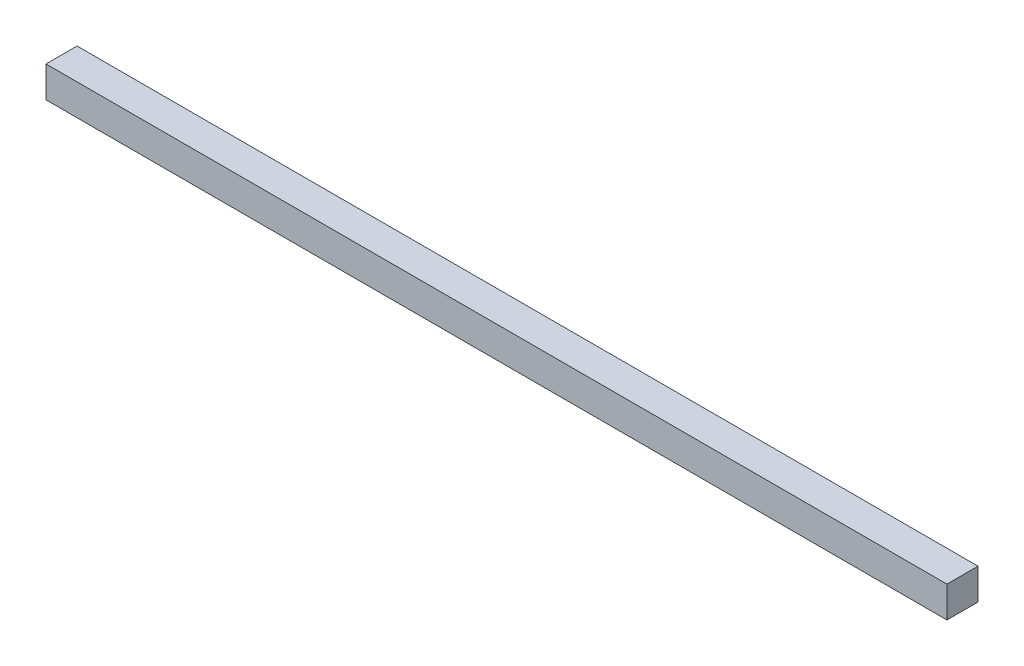
SolidWorks part; units mm, degrees
ref_plane "Front Plane" through (0, 0, 0) normal (0, 0, 1) x (1, 0, 0)
ref_plane "Top Plane" through (0, 0, 0) normal (0, 1, 0) x (1, 0, 0)
ref_plane "Right Plane" through (0, 0, 0) normal (1, 0, 0) x (0, 0, -1)
sketch "Sketch1" plane through (0, 0, 0) normal (0, 0, 1) x (1, 0, 0)
  line L1 (0, 0) -> (36.83, 0)
  line L2 (0, 0) -> (0, 1.27)
  line L3 (0, 1.27) -> (36.83, 1.27)
  line L4 (36.83, 0) -> (36.83, 1.27)
  dimension "D1" = 36.83
  dimension "D2" = 1.27
extrude "Boss-Extrude1" add sketch "Sketch1" along normal blind 1.27
